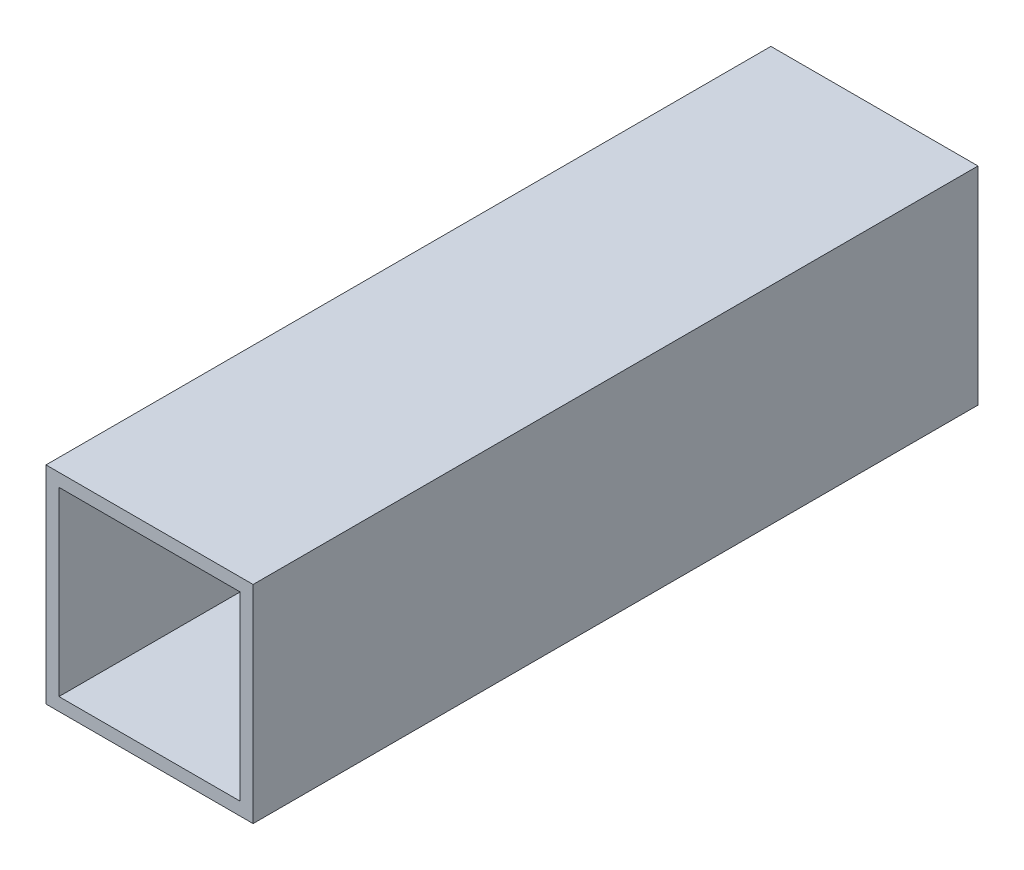
SolidWorks part; units mm, degrees
material "6061-T6 (SS)"
ref_plane "Front Plane" through (0, 0, 0) normal (0, 0, 1) x (1, 0, 0)
ref_plane "Top Plane" through (0, 0, 0) normal (0, 1, 0) x (1, 0, 0)
ref_plane "Right Plane" through (0, 0, 0) normal (1, 0, 0) x (0, 0, -1)
sketch "Sketch1" plane through (0, 0, 0) normal (0, 0, 1) x (1, 0, 0)
  line L0 (3.175, 3.175) -> (3.175, 47.625)
  line L1 (0, 0) -> (50.8, 0)
  line L2 (0, 0) -> (0, 50.8)
  line L3 (0, 50.8) -> (50.8, 50.8)
  line L4 (50.8, 0) -> (50.8, 50.8)
  line L5 (3.175, 47.625) -> (47.625, 47.625)
  line L6 (47.625, 3.175) -> (47.625, 47.625)
  line L7 (3.175, 3.175) -> (47.625, 3.175)
  dimension "D1" = 50.8
  dimension "D2" = 50.8
  dimension "D3" = 3.175
extrude "Boss-Extrude1" add sketch "Sketch1" along normal blind 177.8
